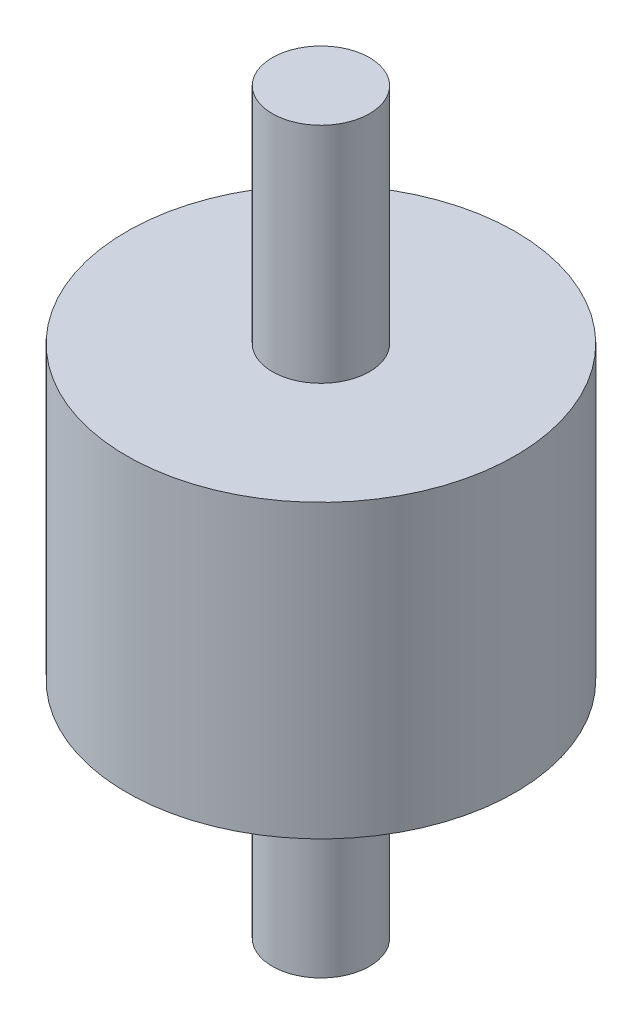
SolidWorks part; units mm, degrees
ref_plane "Front Plane" through (0, 0, 0) normal (0, 0, 1) x (1, 0, 0)
ref_plane "Top Plane" through (0, 0, 0) normal (0, 1, 0) x (1, 0, 0)
ref_plane "Right Plane" through (0, 0, 0) normal (1, 0, 0) x (0, 0, -1)
sketch "Sketch1" plane through (0, 0, 0) normal (0, 0, 1) x (1, 0, 0)
  line L0 (0, 38) -> (5, 38)
  line L1 (5, 38) -> (5, 15)
  line L2 (5, 15) -> (20, 15)
  line L3 (20, 15) -> (20, 0)
  line L4 (20, 0) -> (0, 0)
  line L5 (0, 0) -> (0, 38)
  dimension "D1" = 23
  dimension "D2" = 5
  dimension "D3" = 20
  dimension "D4" = 15
revolve "Revolve1" add sketch "Sketch1" angle 360 about L5
mirror "Mirror1" about plane through (20, 0, 0) normal (0, -1, 0) of "Revolve1"
